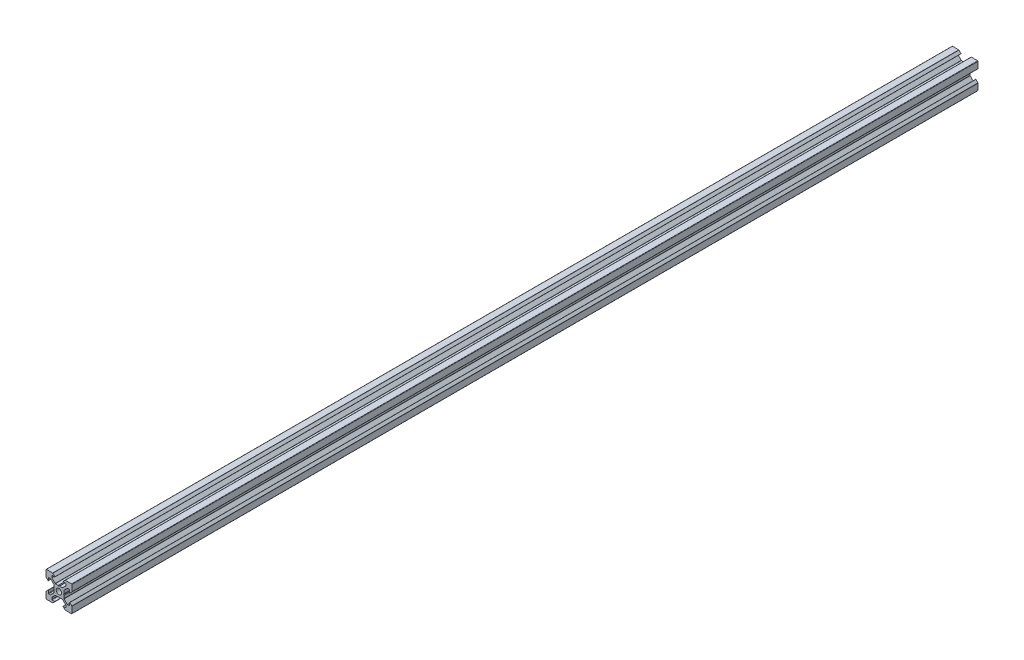
SolidWorks part; units mm, degrees
material "6063-T5"
ref_plane "Plan de face" through (0, 0, 0) normal (0, 0, 1) x (1, 0, 0)
ref_plane "Plan de dessus" through (0, 0, 0) normal (0, 1, 0) x (1, 0, 0)
ref_plane "Plan de droite" through (0, 0, 0) normal (1, 0, 0) x (0, 0, -1)
sketch "Esquisse1" plane through (0, 0, 0) normal (0, 0, 1) x (1, 0, 0)
  line L0 (18.7749, -2.8952) -> (18.7749, -4.8946)
  line L1 (18.4749, -5.1946) -> (17.2591, -5.1946)
  line L2 (17.047, -5.1067) -> (14.5634, -2.6231)
  line L3 (14.4755, -2.411) -> (14.4755, -0.2148)
  line L4 (14.4755, -0.2148) -> (14.1755, 0.3048)
  line L5 (14.1755, 0.3048) -> (14.4755, 0.8244)
  line L6 (14.4755, 0.8244) -> (14.4755, 3.0205)
  line L7 (14.5634, 3.2326) -> (17.047, 5.7162)
  line L8 (17.2591, 5.8041) -> (18.4749, 5.8041)
  line L9 (18.7749, 5.5041) -> (18.7749, 3.5048)
  line L10 (18.9456, 3.4341) -> (20.487, 4.9755)
  line L11 (20.5749, 5.1876) -> (20.5749, 10.0048)
  line L12 (20.2749, 10.3048) -> (15.4577, 10.3048)
  line L13 (15.2456, 10.2169) -> (13.7041, 8.6755)
  line L14 (13.7749, 8.5048) -> (15.7742, 8.5048)
  line L15 (16.0742, 8.2048) -> (16.0742, 6.989)
  line L16 (15.9863, 6.7769) -> (13.5027, 4.2933)
  line L17 (13.2906, 4.2054) -> (11.0945, 4.2054)
  line L18 (11.0945, 4.2054) -> (10.5749, 3.9054)
  line L19 (10.5749, 3.9054) -> (10.0552, 4.2054)
  line L20 (10.0552, 4.2054) -> (7.8591, 4.2054)
  line L21 (7.647, 4.2933) -> (5.1634, 6.7769)
  line L22 (5.0755, 6.989) -> (5.0755, 8.2048)
  line L23 (5.3755, 8.5048) -> (7.3749, 8.5048)
  line L24 (7.4456, 8.6755) -> (5.9041, 10.2169)
  line L25 (5.692, 10.3048) -> (0.8749, 10.3048)
  line L26 (0.5749, 10.0048) -> (0.5749, 5.1876)
  line L27 (0.6627, 4.9755) -> (2.2041, 3.4341)
  line L28 (2.3749, 3.5048) -> (2.3749, 5.5041)
  line L29 (2.6749, 5.8041) -> (3.8906, 5.8041)
  line L30 (4.1027, 5.7162) -> (6.5863, 3.2326)
  line L31 (6.6742, 3.0205) -> (6.6742, 0.8244)
  line L32 (6.6742, 0.8244) -> (6.9742, 0.3048)
  line L33 (6.9742, 0.3048) -> (6.6742, -0.2148)
  line L34 (6.6742, -0.2148) -> (6.6742, -2.411)
  line L35 (6.5863, -2.6231) -> (4.1027, -5.1067)
  line L36 (3.8906, -5.1946) -> (2.6749, -5.1946)
  line L37 (2.3749, -4.8946) -> (2.3749, -2.8952)
  line L38 (2.2041, -2.8245) -> (0.6627, -4.3659)
  line L39 (0.5749, -4.5781) -> (0.5749, -9.3952)
  line L40 (0.8749, -9.6952) -> (5.692, -9.6952)
  line L41 (5.9041, -9.6074) -> (7.4456, -8.0659)
  line L42 (7.3749, -7.8952) -> (5.3755, -7.8952)
  line L43 (5.0755, -7.5952) -> (5.0755, -6.3795)
  line L44 (5.1634, -6.1674) -> (7.647, -3.6838)
  line L45 (7.8591, -3.5959) -> (10.0552, -3.5959)
  line L46 (10.0552, -3.5959) -> (10.5749, -3.2959)
  line L47 (10.5749, -3.2959) -> (11.0945, -3.5959)
  line L48 (11.0945, -3.5959) -> (13.2906, -3.5959)
  line L49 (13.5027, -3.6838) -> (15.9863, -6.1674)
  line L50 (16.0742, -6.3795) -> (16.0742, -7.5952)
  line L51 (15.7742, -7.8952) -> (13.7749, -7.8952)
  line L52 (13.7041, -8.0659) -> (15.2456, -9.6074)
  line L53 (15.4577, -9.6952) -> (20.2749, -9.6952)
  line L54 (20.5749, -9.3952) -> (20.5749, -4.5781)
  line L55 (20.487, -4.3659) -> (18.9456, -2.8245)
  arc A0 (10.5749, -1.7952) -> (12.6749, 0.3048) centre (10.5749, 0.3048) ccw
  arc A1 (12.6749, 0.3048) -> (10.5749, 2.4048) centre (10.5749, 0.3048) ccw
  arc A2 (10.5749, 2.4048) -> (8.4749, 0.3048) centre (10.5749, 0.3048) ccw
  arc A3 (8.4749, 0.3048) -> (10.5749, -1.7952) centre (10.5749, 0.3048) ccw
  arc A4 (18.9456, -2.8245) -> (18.7749, -2.8952) centre (18.8749, -2.8952) ccw
  arc A5 (18.4749, -5.1946) -> (18.7749, -4.8946) centre (18.4749, -4.8946) ccw
  arc A6 (17.047, -5.1067) -> (17.2591, -5.1946) centre (17.2591, -4.8946) ccw
  arc A7 (14.4755, -2.411) -> (14.5634, -2.6231) centre (14.7755, -2.411) ccw
  arc A8 (14.5634, 3.2326) -> (14.4755, 3.0205) centre (14.7755, 3.0205) ccw
  arc A9 (17.2591, 5.8041) -> (17.047, 5.7162) centre (17.2591, 5.5041) ccw
  arc A10 (18.7749, 5.5041) -> (18.4749, 5.8041) centre (18.4749, 5.5041) ccw
  arc A11 (18.7749, 3.5048) -> (18.9456, 3.4341) centre (18.8749, 3.5048) ccw
  arc A12 (20.487, 4.9755) -> (20.5749, 5.1876) centre (20.2749, 5.1876) ccw
  arc A13 (20.5749, 10.0048) -> (20.2749, 10.3048) centre (20.2749, 10.0048) ccw
  arc A14 (15.4577, 10.3048) -> (15.2456, 10.2169) centre (15.4577, 10.0048) ccw
  arc A15 (13.7041, 8.6755) -> (13.7749, 8.5048) centre (13.7749, 8.6048) ccw
  arc A16 (16.0742, 8.2048) -> (15.7742, 8.5048) centre (15.7742, 8.2048) ccw
  arc A17 (15.9863, 6.7769) -> (16.0742, 6.989) centre (15.7742, 6.989) ccw
  arc A18 (13.2906, 4.2054) -> (13.5027, 4.2933) centre (13.2906, 4.5054) ccw
  arc A19 (7.647, 4.2933) -> (7.8591, 4.2054) centre (7.8591, 4.5054) ccw
  arc A20 (5.0755, 6.989) -> (5.1634, 6.7769) centre (5.3755, 6.989) ccw
  arc A21 (5.3755, 8.5048) -> (5.0755, 8.2048) centre (5.3755, 8.2048) ccw
  arc A22 (7.3749, 8.5048) -> (7.4456, 8.6755) centre (7.3749, 8.6048) ccw
  arc A23 (5.9041, 10.2169) -> (5.692, 10.3048) centre (5.692, 10.0048) ccw
  arc A24 (0.8749, 10.3048) -> (0.5749, 10.0048) centre (0.8749, 10.0048) ccw
  arc A25 (0.5749, 5.1876) -> (0.6627, 4.9755) centre (0.8749, 5.1876) ccw
  arc A26 (2.2041, 3.4341) -> (2.3749, 3.5048) centre (2.2749, 3.5048) ccw
  arc A27 (2.6749, 5.8041) -> (2.3749, 5.5041) centre (2.6749, 5.5041) ccw
  arc A28 (4.1027, 5.7162) -> (3.8906, 5.8041) centre (3.8906, 5.5041) ccw
  arc A29 (6.6742, 3.0205) -> (6.5863, 3.2326) centre (6.3742, 3.0205) ccw
  arc A30 (6.5863, -2.6231) -> (6.6742, -2.411) centre (6.3742, -2.411) ccw
  arc A31 (3.8906, -5.1946) -> (4.1027, -5.1067) centre (3.8906, -4.8946) ccw
  arc A32 (2.3749, -4.8946) -> (2.6749, -5.1946) centre (2.6749, -4.8946) ccw
  arc A33 (2.3749, -2.8952) -> (2.2041, -2.8245) centre (2.2749, -2.8952) ccw
  arc A34 (0.6627, -4.3659) -> (0.5749, -4.5781) centre (0.8749, -4.5781) ccw
  arc A35 (0.5749, -9.3952) -> (0.8749, -9.6952) centre (0.8749, -9.3952) ccw
  arc A36 (5.692, -9.6952) -> (5.9041, -9.6074) centre (5.692, -9.3952) ccw
  arc A37 (7.4456, -8.0659) -> (7.3749, -7.8952) centre (7.3749, -7.9952) ccw
  arc A38 (5.0755, -7.5952) -> (5.3755, -7.8952) centre (5.3755, -7.5952) ccw
  arc A39 (5.1634, -6.1674) -> (5.0755, -6.3795) centre (5.3755, -6.3795) ccw
  arc A40 (7.8591, -3.5959) -> (7.647, -3.6838) centre (7.8591, -3.8959) ccw
  arc A41 (13.5027, -3.6838) -> (13.2906, -3.5959) centre (13.2906, -3.8959) ccw
  arc A42 (16.0742, -6.3795) -> (15.9863, -6.1674) centre (15.7742, -6.3795) ccw
  arc A43 (15.7742, -7.8952) -> (16.0742, -7.5952) centre (15.7742, -7.5952) ccw
  arc A44 (13.7749, -7.8952) -> (13.7041, -8.0659) centre (13.7749, -7.9952) ccw
  arc A45 (15.2456, -9.6074) -> (15.4577, -9.6952) centre (15.4577, -9.3952) ccw
  arc A46 (20.2749, -9.6952) -> (20.5749, -9.3952) centre (20.2749, -9.3952) ccw
  arc A47 (20.5749, -4.5781) -> (20.487, -4.3659) centre (20.2749, -4.5781) ccw
extrude "Boss.-Extru.1" add sketch "Esquisse1" along normal blind 700
